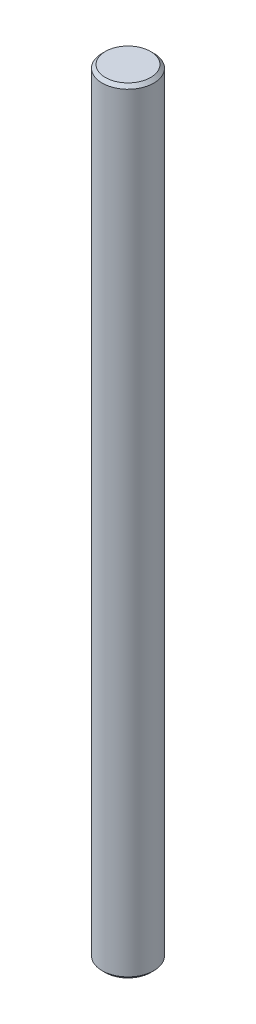
SolidWorks part; units mm, degrees
ref_plane "Front Plane" through (0, 0, 0) normal (0, 0, 1) x (1, 0, 0)
ref_plane "Top Plane" through (0, 0, 0) normal (0, 1, 0) x (1, 0, 0)
ref_plane "Right Plane" through (0, 0, 0) normal (1, 0, 0) x (0, 0, -1)
sketch "Sketch1" plane through (0, 0, 0) normal (0, 1, 0) x (1, 0, 0)
  circle A0 centre (0, 0) radius 2
  dimension "D1" = 4
extrude "Boss-Extrude1" add sketch "Sketch1" along normal mid plane 60
chamfer "Chamfer1" distance 0.25 angle 45 2 edges at (0, -30, 2) (0, 30, 2)
